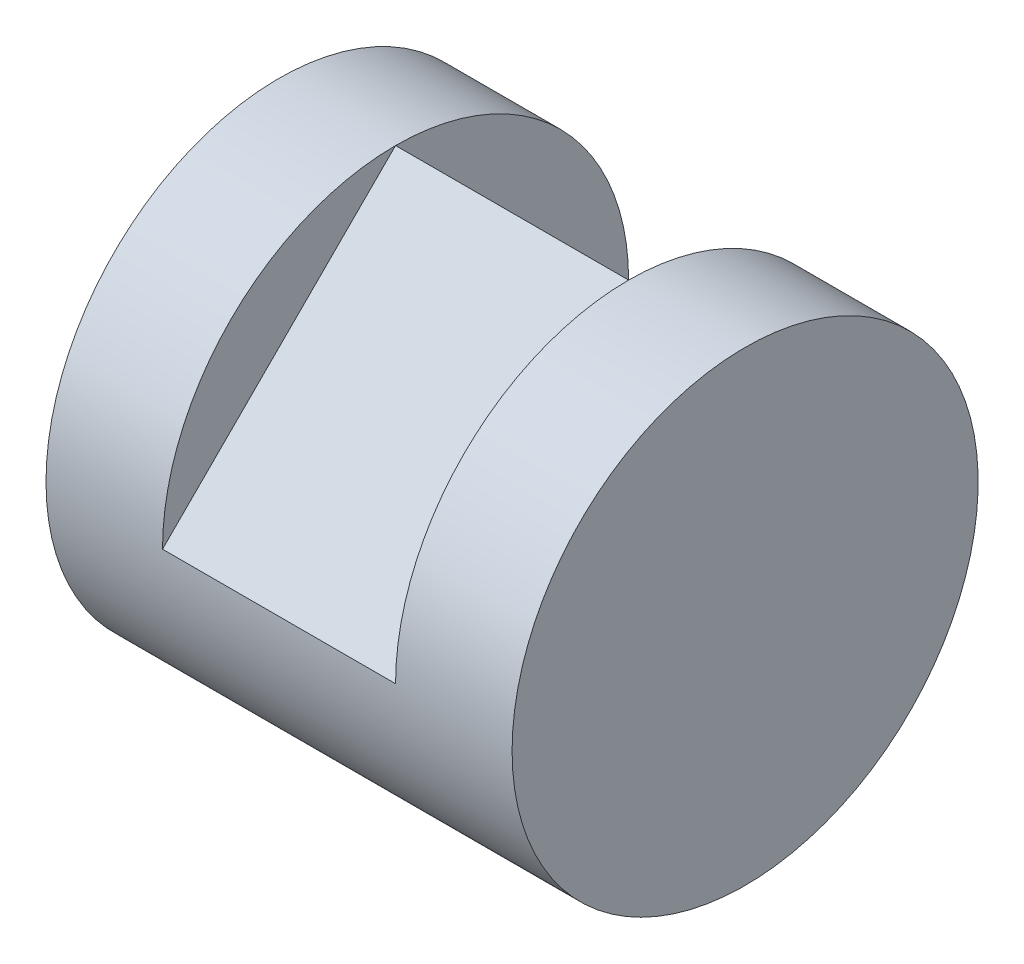
SolidWorks part; units mm, degrees
ref_plane "Front Plane" through (0, 0, 0) normal (0, 0, 1) x (1, 0, 0)
ref_plane "Top Plane" through (0, 0, 0) normal (0, 1, 0) x (1, 0, 0)
ref_plane "Right Plane" through (0, 0, 0) normal (1, 0, 0) x (0, 0, -1)
sketch "Sketch1" plane through (0, 0, 0) normal (0, 0, 1) x (1, 0, 0)
  line L1 (0, 0) -> (40, 0)
  line L2 (0, 0) -> (0, 40)
  line L3 (0, 40) -> (40, 40)
  line L4 (40, 0) -> (40, 40)
  dimension "D1" = 40
  dimension "D2" = 40
extrude "Boss-Extrude1" add sketch "Sketch1" along normal blind 40
sketch "Sketch2" plane through (0, 0, 0) normal (-1, 0, 0) x (0, 0, 1)
  line L0 (0, 40) -> (0, 0) construction
  line L1 (40, 0) -> (0, 0) construction
  line L3 (0, 40) -> (40, 40)
  line L4 (0, 40) -> (0, 0)
  line L5 (0, 0) -> (40, 0)
  line L6 (40, 40) -> (40, 0)
  circle A0 centre (20, 20) radius 20
  line M1 (0, 40) -> (0, 0)
  line M2 (0, 0) -> (40, 0)
  line M3 (40, 0) -> (40, 40)
  line M4 (40, 40) -> (0, 40)
  dimension "D1" = 40
extrude "Cut-Extrude1" cut sketch "Sketch2" against normal blind 71 contours A0 L3 M1 | A0 L6 M4 | A0 L5 M3 | A0 L4 M2
sketch "Sketch3" plane through (0, 0, 0) normal (0, 0, 1) x (1, 0, 0)
  line L0 (40, 40) -> (0, 40) construction
  line L1 (10, 40) -> (30, 40)
  line L2 (10, 40) -> (10, 20)
  line L3 (10, 20) -> (30, 20)
  line L4 (30, 40) -> (30, 20)
  line L5 (0, 40) -> (0, 0) construction
  dimension "D1" = 20
  dimension "D2" = 20
  dimension "D3" = 10
extrude "Cut-Extrude2" cut sketch "Sketch3" along normal blind 71
sketch "Sketch4" plane through (10, 0, 0) normal (1, 0, 0) x (0, 0, -1)
  line L0 (-20, 20) -> (-20, 40)
  line L1 (-20, 40) -> (-40, 20)
  line L2 (-40, 20) -> (-20, 20)
  line L3 (0, 20) -> (-20, 20)
  line L4 (-20, 40) -> (0, 20)
  arc A0 (0, 20) -> (-40, 20) centre (-20, 20) ccw construction
  line M2 (-40, 20) -> (0, 20)
extrude "Boss-Extrude2" add sketch "Sketch4" along normal blind 20 contours L0 L1 M2 | L4 L0 M2
